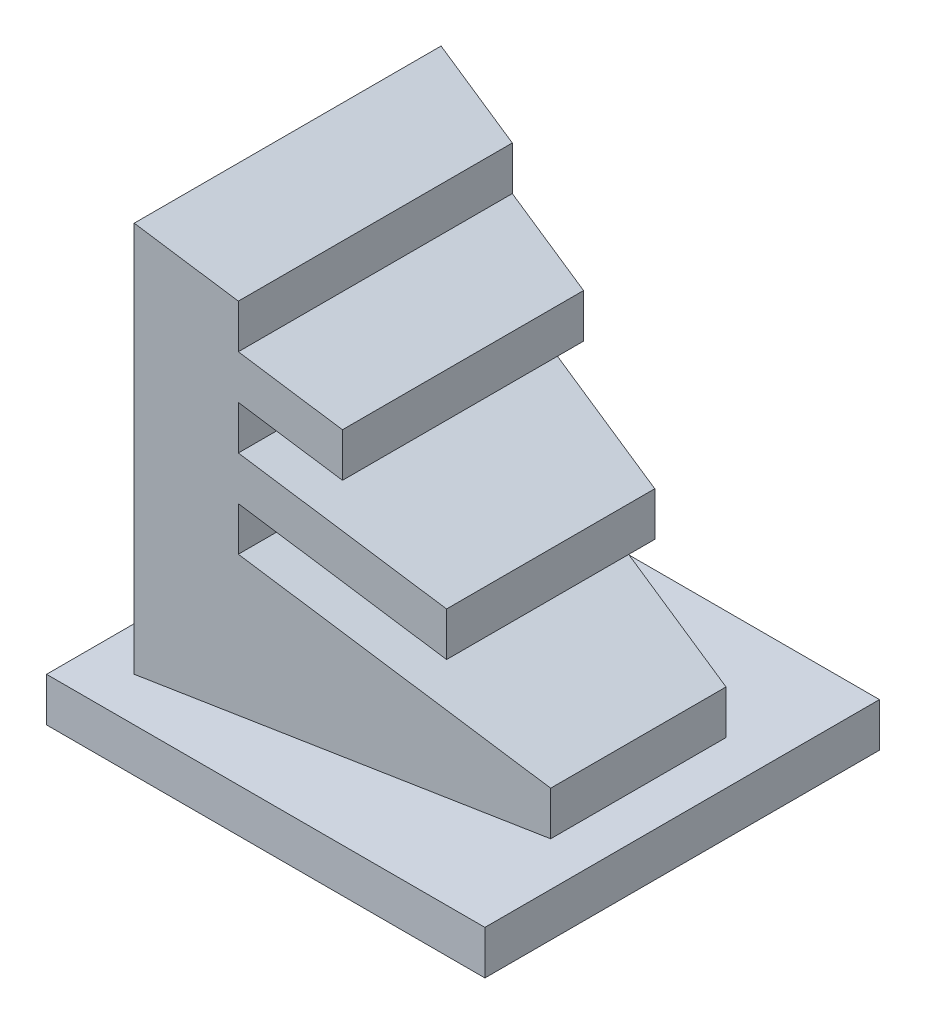
SolidWorks part; units mm, degrees
other "Perspective"
ref_plane "Front Plane" through (0, 0, 0) normal (0, 0, 1) x (1, 0, 0)
ref_plane "Top Plane" through (0, 0, 0) normal (0, 1, 0) x (1, 0, 0)
ref_plane "Right Plane" through (0, 0, 0) normal (1, 0, 0) x (0, 0, -1)
sketch "Sketch1" plane through (0, 0, 0) normal (0, 1, 0) x (1, 0, 0)
  line L1 (-90, 65) -> (10, 65)
  line L2 (-90, 65) -> (-90, -25)
  line L3 (-90, -25) -> (10, -25)
  line L4 (10, 65) -> (10, -25)
  dimension "D1" = 90
  dimension "D2" = 100
  dimension "D3" = 10
  dimension "D4" = 25
extrude "Extrude1" add sketch "Sketch1" along normal blind 10
sketch "Sketch2" plane through (0, 10, 0) normal (0, 1, 0) x (1, 0, 0)
  line L0 (0, 0) -> (0, 40)
  line L1 (0, 40) -> (-80, 55)
  line L2 (-80, 55) -> (-80, -15)
  line L3 (-80, -15) -> (0, 0)
  line L4 (10, 65) -> (-90, 65) construction
  line L5 (-90, -25) -> (10, -25) construction
  line L6 (55.3232, -15) -> (135.3232, -15) construction
  line L7 (135.3232, -15) -> (135.3232, 45) construction
  line L8 (135.3232, 45) -> (55.3232, 74.1176) construction
  line L9 (55.3232, 74.1176) -> (55.3232, -15) construction
  line L10 (55.3232, 74.1176) -> (135.3232, 74.1176) construction
  line L11 (135.3232, 74.1176) -> (135.3232, 45) construction
  line L12 (135.3232, -5) -> (75.3232, 16.8382) construction
  line L13 (75.3232, 16.8382) -> (75.3232, 66.8382) construction
  dimension "D1" = 40
  dimension "D2" = 80
  dimension "D3" = 10
  dimension "D4" = 10
  dimension "D5" = 80
  dimension "D6" = 20
  dimension "D7" = 10
  dimension "D8" = 20
  dimension "D9" = 50
  dimension "D10" = 89.1176
extrude "Extrude2" add sketch "Sketch2" along normal blind 89.118
sketch "Sketch3" plane through (0, 0, 0) normal (0, 0, 1) x (1, 0, 0)
  line L0 (-80, 99.118) -> (-60, 91.8386)
  line L1 (-40, 74.5592) -> (-40, 64.5592)
  line L2 (-40, 74.5592) -> (-60, 81.8386)
  line L3 (-60, 51.8386) -> (-60, 41.8386)
  line L4 (-60, 71.8386) -> (-40, 64.5592)
  line L5 (-60, 71.8386) -> (-60, 61.8386)
  line L6 (-20, 47.2798) -> (-60, 61.8386)
  line L8 (-60, 51.8386) -> (-20, 37.2798)
  line L9 (0, 30.0004) -> (0, 20.0004)
  line L10 (0, 20.0004) -> (-60, 41.8386)
  line L13 (0, 99.118) -> (0, 10) construction
  line L14 (0, 10.0004) -> (0, 99.118)
  line L15 (0, 99.118) -> (-80, 99.118)
  line L18 (-60, 81.8386) -> (-60, 91.8386)
  line L19 (-20, 47.2798) -> (-20, 37.2798)
  dimension "D1" = 20
  dimension "D2" = 20
  dimension "D3" = 20
  dimension "D4" = 10
  dimension "D5" = 10
  dimension "D6" = 10
  dimension "D7" = 10
  dimension "D8" = 20
  dimension "D9" = 10
extrude "Extrude3" cut sketch "Sketch3" against normal mid plane 129.118 contours L6 L19 L8 L3 L10 L9 L14 L15 L0 L18 L2 L1 L4 L5
